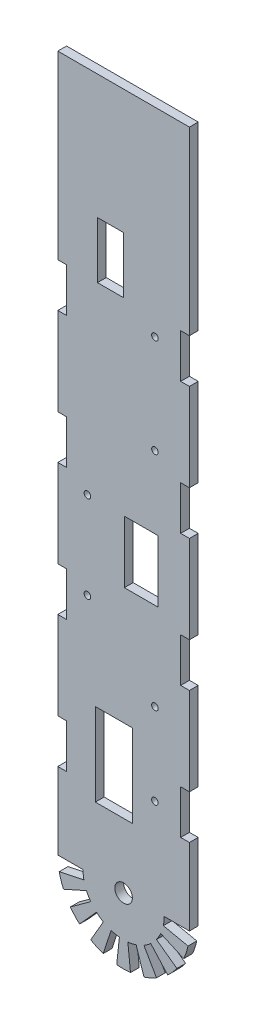
SolidWorks part; units mm, degrees
material "1060 Alloy"
ref_plane "Front Plane" through (0, 0, 0) normal (0, 0, 1) x (1, 0, 0)
ref_plane "Top Plane" through (0, 0, 0) normal (0, 1, 0) x (1, 0, 0)
ref_plane "Right Plane" through (0, 0, 0) normal (1, 0, 0) x (0, 0, -1)
sketch "Sketch1" plane through (0, 0, 0) normal (0, 0, 1) x (1, 0, 0)
  line L0 (-30, 34.9376) -> (-30, 0)
  line L1 (0, 317.2805) -> (0, 260.6261) construction
  line L2 (30, 317.2805) -> (30, 234.9376)
  line L3 (30, 317.2805) -> (-30, 317.2805)
  line L4 (18.5, 0) -> (30, 0)
  line L5 (-30, 317.2805) -> (30, 317.2805)
  line L6 (-11.9247, 260.6261) -> (0, 260.6261)
  line L7 (-11.9247, 260.6261) -> (-11.9247, 234.9355)
  line L8 (-11.9247, 234.9355) -> (0, 234.9355)
  line L9 (0, 260.6261) -> (0, 234.9355)
  line L10 (0.3306, 148.8989) -> (15.5956, 148.8989)
  line L11 (0.3306, 148.8989) -> (0.3306, 120.6731)
  line L12 (0.3306, 120.6731) -> (15.5956, 120.6731)
  line L13 (19.5, 280.1261) -> (0, 280.1261) construction
  line L14 (30, 234.9376) -> (26, 234.9355)
  line L15 (26, 234.9355) -> (26, 214.9355)
  line L16 (26, 214.9355) -> (30, 214.9376)
  line L17 (30, 214.9376) -> (30, 174.9376)
  line L18 (26, 174.9355) -> (30, 174.9376)
  line L19 (26, 174.9355) -> (26, 154.9355)
  line L20 (26, 154.9355) -> (30, 154.9376)
  line L21 (30, 154.9376) -> (30, 114.9376)
  line L22 (26, 114.9355) -> (30, 114.9376)
  line L23 (26, 114.9355) -> (26, 94.9355)
  line L24 (26, 94.9355) -> (30, 94.9376)
  line L25 (30, 94.9376) -> (30, 54.9376)
  line L26 (26, 54.9355) -> (30, 54.9376)
  line L27 (26, 54.9355) -> (26, 34.9355)
  line L28 (26, 34.9355) -> (30, 34.9376)
  line L29 (30, 34.9376) -> (30, 0)
  line L30 (-26, 34.9355) -> (-30, 34.9376)
  line L31 (-26, 54.9355) -> (-26, 34.9355)
  line L32 (-26, 54.9355) -> (-30, 54.9376)
  line L33 (-30, 94.9376) -> (-30, 54.9376)
  line L34 (-26, 94.9355) -> (-30, 94.9376)
  line L35 (-26, 114.9355) -> (-26, 94.9355)
  line L36 (-26, 114.9355) -> (-30, 114.9376)
  line L37 (-30, 154.9376) -> (-30, 114.9376)
  line L38 (-26, 154.9355) -> (-30, 154.9376)
  line L39 (-26, 174.9355) -> (-26, 154.9355)
  line L40 (-26, 174.9355) -> (-30, 174.9376)
  line L41 (-30, 214.9376) -> (-30, 174.9376)
  line L42 (-26, 214.9355) -> (-30, 214.9376)
  line L43 (-26, 234.9355) -> (-26, 214.9355)
  line L44 (-30, 234.9376) -> (-26, 234.9355)
  line L45 (-30, 317.2805) -> (-30, 234.9376)
  line L46 (0, 4) -> (0, 0) construction
  line L47 (-19.5, 280.1261) -> (-20.2775, 280.1261) construction
  line L48 (15.5956, 148.8989) -> (15.5956, 120.6731)
  line L49 (-12.8754, 67.1702) -> (4, 67.1702)
  line L50 (-12.8754, 67.1702) -> (-12.8754, 29.4456)
  line L51 (-12.8754, 29.4456) -> (4, 29.4456)
  line L52 (4, 67.1702) -> (4, 29.4456)
  line L53 (18.0957, -3.8464) -> (29.3444, -6.2374)
  line L54 (16.9006, -7.5246) -> (27.4064, -12.2021)
  line L55 (14.9668, -10.874) -> (24.2705, -17.6336)
  line L56 (12.3789, -13.7482) -> (20.0739, -22.2943)
  line L57 (9.25, -16.0215) -> (15, -25.9808)
  line L58 (5.7168, -17.5945) -> (9.2705, -28.5317)
  line L59 (1.9338, -18.3987) -> (3.1359, -29.8357)
  line L60 (-1.9338, -18.3987) -> (-3.1359, -29.8357)
  line L61 (-5.7168, -17.5945) -> (-9.2705, -28.5317)
  line L62 (-9.25, -16.0215) -> (-15, -25.9808)
  line L63 (-12.3789, -13.7482) -> (-20.0739, -22.2943)
  line L64 (-14.9668, -10.874) -> (-24.2705, -17.6336)
  line L65 (-16.9006, -7.5246) -> (-27.4064, -12.2021)
  line L66 (-18.0957, -3.8464) -> (-29.3444, -6.2374)
  line L67 (-18.5, 0) -> (-30, 0)
  arc A0 (-29.3444, -6.2374) -> (-27.4064, -12.2021) centre (0, 0) ccw
  circle A1 centre (14.2729, 226.6267) radius 1.5
  circle A2 centre (0, 0) radius 4
  circle A3 centre (14.2729, 181.7435) radius 1.5
  circle A4 centre (-16.5, 148.8989) radius 1.5
  circle A5 centre (-16.5, 109.236) radius 1.5
  circle A6 centre (14.2729, 80.662) radius 1.5
  circle A7 centre (14.2729, 43.3928) radius 1.5
  arc A8 (18.0957, -3.8464) -> (18.5, 0) centre (0, 0) ccw
  arc A9 (14.9668, -10.874) -> (16.9006, -7.5246) centre (0, 0) ccw
  arc A10 (27.4064, -12.2021) -> (29.3444, -6.2374) centre (0, 0) ccw
  arc A11 (9.25, -16.0215) -> (12.3789, -13.7482) centre (0, 0) ccw
  arc A12 (20.0739, -22.2943) -> (24.2705, -17.6336) centre (0, 0) ccw
  arc A13 (1.9338, -18.3987) -> (5.7168, -17.5945) centre (0, 0) ccw
  arc A14 (9.2705, -28.5317) -> (15, -25.9808) centre (0, 0) ccw
  arc A15 (-5.7168, -17.5945) -> (-1.9338, -18.3987) centre (0, 0) ccw
  arc A16 (-3.1359, -29.8357) -> (3.1359, -29.8357) centre (0, 0) ccw
  arc A17 (-15, -25.9808) -> (-9.2705, -28.5317) centre (0, 0) ccw
  arc A18 (-12.3789, -13.7482) -> (-9.25, -16.0215) centre (0, 0) ccw
  arc A19 (-16.9006, -7.5246) -> (-14.9668, -10.874) centre (0, 0) ccw
  arc A20 (-24.2705, -17.6336) -> (-20.0739, -22.2943) centre (0, 0) ccw
  arc A21 (-18.5, 0) -> (-18.0957, -3.8464) centre (0, 0) ccw
  point P103 (0, 0)
  point P111 (0, 0)
  dimension "D2" = 16
  dimension "D15" = 4
  dimension "D16" = 20
  dimension "D17" = 40
extrude "Boss-Extrude1" add sketch "Sketch1" along normal blind 4
